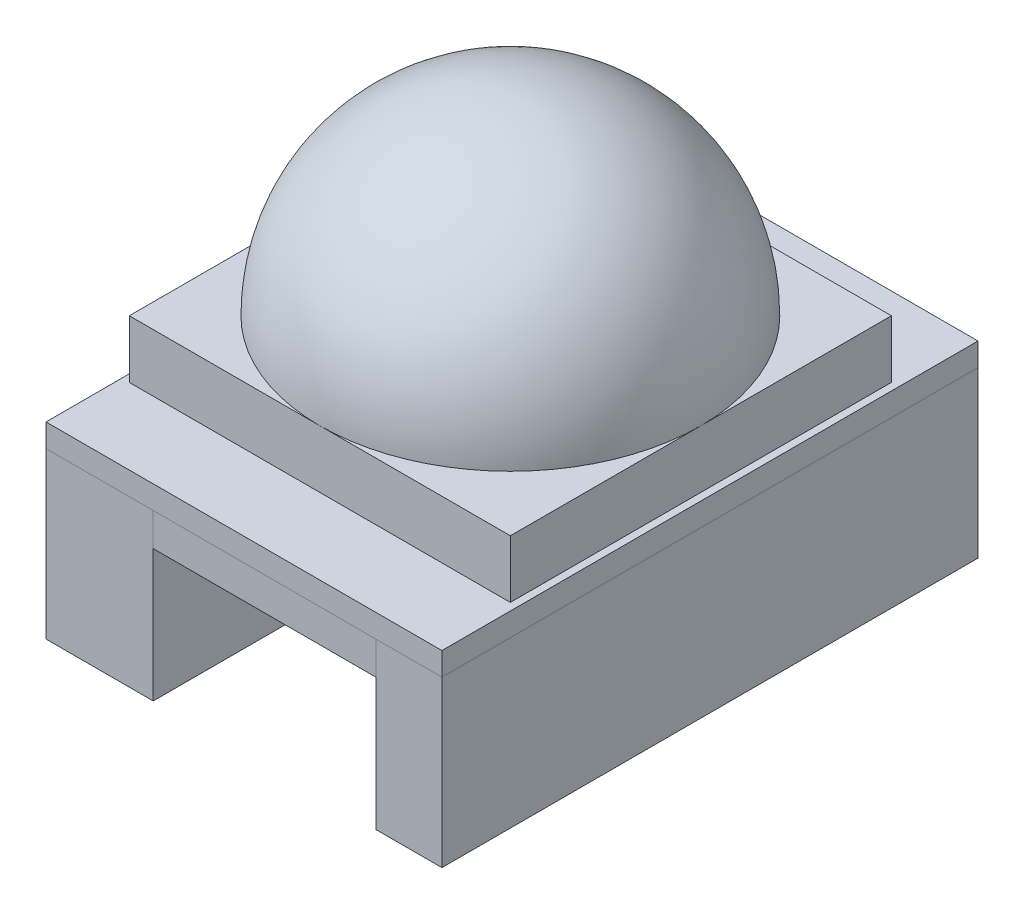
SolidWorks part; units mm, degrees
ref_plane "Front Plane" through (0, 0, 0) normal (0, 0, 1) x (1, 0, 0)
ref_plane "Top Plane" through (0, 0, 0) normal (0, 1, 0) x (1, 0, 0)
ref_plane "Right Plane" through (0, 0, 0) normal (1, 0, 0) x (0, 0, -1)
sketch "Sketch1" plane through (0, 0, 0) normal (0, 1, 0) x (1, 0, 0)
  line L1 (-10.4392, 6.6013) -> (13.5608, 6.6013)
  line L2 (-10.4392, 6.6013) -> (-10.4392, -25.8987)
  line L3 (-10.4392, -25.8987) -> (13.5608, -25.8987)
  line L4 (13.5608, 6.6013) -> (13.5608, -25.8987)
  dimension "D1" = 24
  dimension "D2" = 32.5
extrude "Boss-Extrude1" add sketch "Sketch1" along normal blind 1.4
sketch "Sketch2" plane through (0, 1.4, 0) normal (0, 1, 0) x (1, 0, 0)
  line L0 (-10.4392, -25.8987) -> (13.5608, -25.8987) construction
  line L1 (-9.9892, 1.8013) -> (13.1108, 1.8013)
  line L2 (-9.9892, 1.8013) -> (-9.9892, -21.2987)
  line L3 (-9.9892, -21.2987) -> (13.1108, -21.2987)
  line L4 (13.1108, 1.8013) -> (13.1108, -21.2987)
  line L5 (13.5608, 6.6013) -> (-10.4392, 6.6013) construction
  point P4 (1.5608, -21.2987)
  point P7 (1.5608, -25.8987)
  dimension "D1" = 23.1
  dimension "D2" = 23.1
  dimension "D3" = 0
  dimension "D4" = 27.9
extrude "Boss-Extrude2" add sketch "Sketch2" along normal blind 3.5
sketch "Sketch3" plane through (0, 4.9, 0) normal (0, 1, 0) x (1, 0, 0)
  line L0 (1.5608, 1.8013) -> (1.5608, -21.2987) construction
  line L1 (13.1108, 1.8013) -> (-9.9892, 1.8013) construction
  line L2 (-9.9892, -21.2987) -> (13.1108, -21.2987) construction
  line L3 (-9.9892, -9.7487) -> (13.1108, -9.7487) construction
  line L4 (-9.9892, 1.8013) -> (-9.9892, -21.2987) construction
  line L5 (13.1108, -21.2987) -> (13.1108, 1.8013) construction
  circle A0 centre (1.5608, -9.7487) radius 11.55
ref_plane "Plane1" through (0, 0, 9.7487) normal (0, 0, 1) x (1, 0, 0)
sketch "Sketch4" plane through (0, 0, 9.7487) normal (0, 0, 1) x (1, 0, 0)
  line L0 (13.1108, 4.9) -> (-9.9892, 4.9) construction
  line L1 (-9.9892, 4.9) -> (1.5608, 4.9)
  line L2 (1.5608, 4.9) -> (1.5608, 16.45)
  arc A0 (1.5608, 16.45) -> (-9.9892, 4.9) centre (1.5608, 4.9) ccw
revolve "Revolve1" add sketch "Sketch4" angle 360 about L2
sketch "Sketch5" plane through (0, 0, 0) normal (0, -1, 0) x (1, 0, 0)
  line L0 (13.5608, -6.6013) -> (-10.4392, -6.6013) construction
  line L1 (-10.4392, 25.8987) -> (-3.9392, 25.8987)
  line L2 (-10.4392, 25.8987) -> (-10.4392, -6.6013)
  line L3 (-10.4392, -6.6013) -> (-3.9392, -6.6013)
  line L4 (-3.9392, 25.8987) -> (-3.9392, -6.6013)
  line L6 (13.5608, 25.8987) -> (9.5608, 25.8987)
  line L7 (13.5608, 25.8987) -> (13.5608, -6.6013)
  line L8 (13.5608, -6.6013) -> (9.5608, -6.6013)
  line L9 (9.5608, 25.8987) -> (9.5608, -6.6013)
  dimension "D1" = 4
  dimension "D2" = 6.5
extrude "Boss-Extrude5" add sketch "Sketch5" along normal blind 10 separate body
sketch "Sketch6" plane through (0, 0, 0) normal (0, -1, 0) x (1, 0, 0)
  line L1 (-3.9392, 25.8987) -> (9.5608, 25.8987)
  line L2 (-3.9392, 25.8987) -> (-3.9392, -6.6013)
  line L3 (-3.9392, -6.6013) -> (9.5608, -6.6013)
  line L4 (9.5608, 25.8987) -> (9.5608, -6.6013)
extrude "Boss-Extrude6" add sketch "Sketch6" along normal blind 2 separate body
